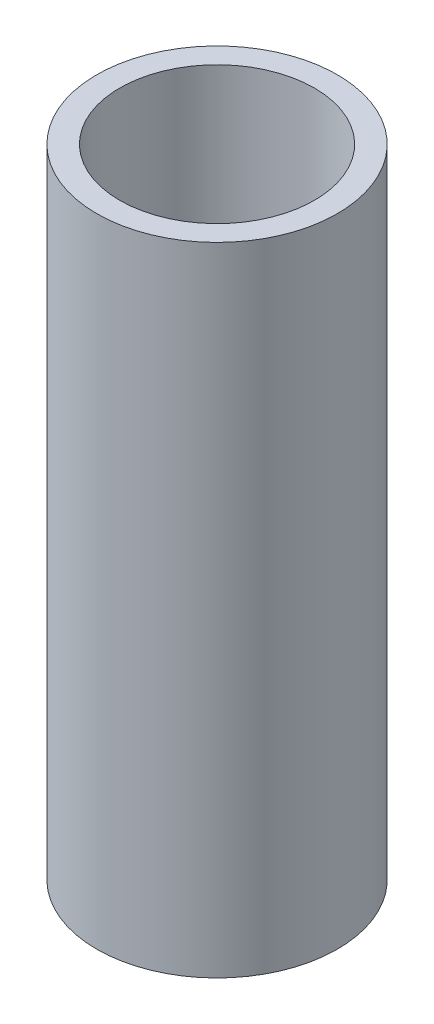
SolidWorks part; units mm, degrees
material "6061 Alloy"
ref_plane "Front Plane" through (0, 0, 0) normal (0, 0, 1) x (1, 0, 0)
ref_plane "Top Plane" through (0, 0, 0) normal (0, 1, 0) x (1, 0, 0)
ref_plane "Right Plane" through (0, 0, 0) normal (1, 0, 0) x (0, 0, -1)
sketch "Sketch1" plane through (0, 0, 0) normal (0, 1, 0) x (1, 0, 0)
  circle A0 centre (0, 0) radius 34
  dimension "D1" = 68
extrude "Boss-Extrude1" add sketch "Sketch1" along normal blind 180
sketch "Sketch2" plane through (0, 0, 0) normal (0, -1, 0) x (1, 0, 0)
  circle A0 centre (0, 0) radius 27.5
  dimension "D1" = 55
extrude "Cut-Extrude1" cut sketch "Sketch2" against normal through all
ref_plane "Plane1" through (0, 39, 0) normal (0, -1, 0) x (-1, 0, 0)
sketch "Sketch3" plane through (0, 39, 0) normal (0, -1, 0) x (-1, 0, 0)
  circle A0 centre (0, 0) radius 27.5 construction
  circle A2 centre (0, 0) radius 27.5
  circle A4 centre (0, 0) radius 28.5
  dimension "D1" = 1
extrude "Cut-Extrude2" cut sketch "Sketch3" along normal blind 2
